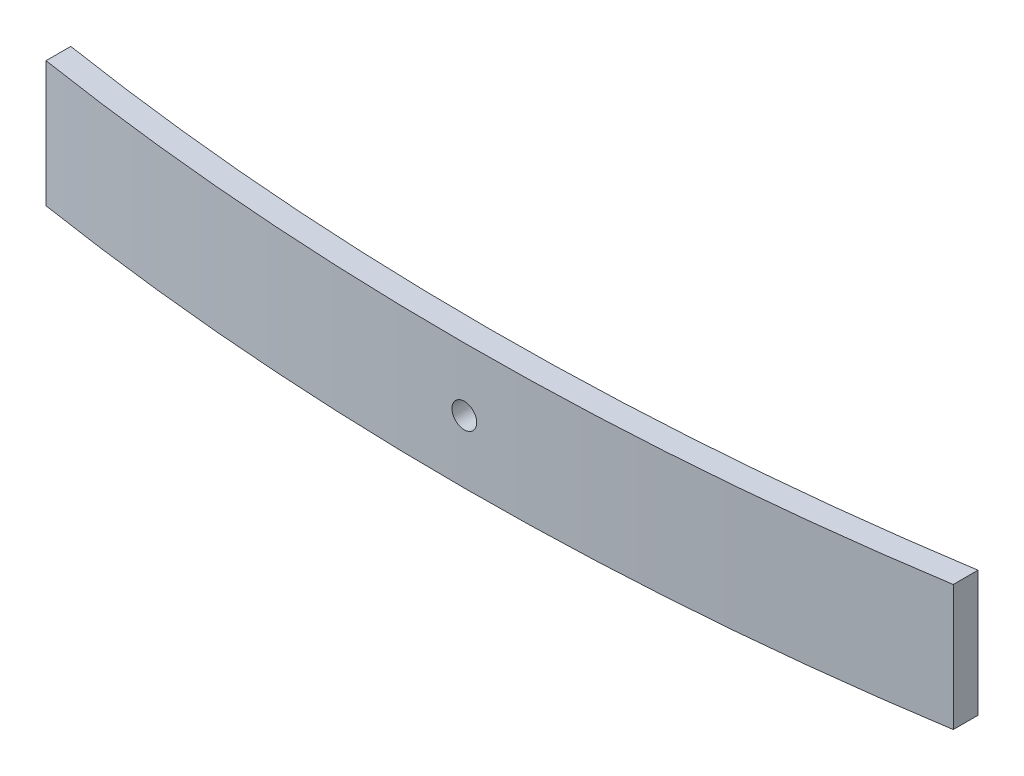
SolidWorks part; units mm, degrees
ref_plane "Front Plane" through (0, 0, 0) normal (0, 0, 1) x (1, 0, 0)
ref_plane "Top Plane" through (0, 0, 0) normal (0, 1, 0) x (1, 0, 0)
ref_plane "Right Plane" through (0, 0, 0) normal (1, 0, 0) x (0, 0, -1)
sketch "Sketch1" plane through (0, 0, 0) normal (0, 1, 0) x (1, 0, 0)
  line L0 (-630, 0) -> (630, 0) construction
  line L1 (-210.8013, -133) -> (245.5549, -133) construction
  line L2 (0, 0) -> (0, -133) construction
  line L3 (-602.5798, 17.4465) -> (-589.9243, 25.4988)
  line L4 (-616.835, -11.5296) -> (-605.5506, -21.4121)
  line L5 (616.835, -11.5296) -> (605.5506, -21.4121)
  line L6 (-630.0217, -47.5) -> (-630.0217, -62.5)
  line L7 (602.5798, 17.4465) -> (589.9243, 25.4988)
  line L8 (630.0217, -47.5) -> (630.0217, -62.5)
  line L9 (-545.0217, -92.3065) -> (-545.0217, -107.3065)
  line L10 (545.0217, -92.3065) -> (545.0217, -107.3065)
  line L11 (-485.0217, -125.4896) -> (-485.0217, -140.4896)
  line L12 (485.0217, -125.4896) -> (485.0217, -140.4896)
  line L13 (-425.0217, -156.3949) -> (-425.0217, -171.3949)
  line L14 (425.0217, -156.3949) -> (425.0217, -171.3949)
  line L15 (-315.0217, -194.8387) -> (-315.0217, -209.8387)
  line L16 (315.0217, -194.8387) -> (315.0217, -209.8387)
  line L17 (-275.0217, -216.5772) -> (-275.0217, -231.5772)
  line L18 (275.0217, -216.5772) -> (275.0217, -231.5772)
  arc A0 (-616.835, -11.5296) -> (-630, -17.5) centre (-630, 0) ccw
  arc A1 (630, -17.5) -> (616.835, -11.5296) centre (630, 0) ccw
  arc A2 (-630, -17.5) -> (630, -17.5) centre (0, 1642.9318) ccw
  arc A3 (-630.0011, -32.5) -> (630.0011, -32.5) centre (0, 1627.9379) ccw
  arc A4 (-605.5506, -21.4121) -> (-630.0011, -32.5) centre (-630, 0) ccw
  arc A5 (630.0011, -32.5) -> (605.5506, -21.4121) centre (630, 0) ccw
  arc A6 (-630.0217, -47.5) -> (630.0217, -47.5) centre (0, 1613.05) ccw
  arc A7 (630.0217, -47.5) -> (589.9243, 25.4988) centre (630, 0) ccw
  arc A8 (-589.9243, 25.4988) -> (-630.0217, -47.5) centre (-630, 0) ccw
  arc A9 (-630.0217, -62.5) -> (630.0217, -62.5) centre (0, 1598.05) ccw
  arc A10 (545.0217, -107.3065) -> (-545.0217, -107.3065) centre (0, 1583.05) cw
  arc A11 (485.0217, -140.4896) -> (-485.0217, -140.4896) centre (0, 1568.05) cw
  arc A12 (425.0217, -171.3949) -> (-425.0217, -171.3949) centre (0, 1553.05) cw
  arc A13 (315.0217, -209.8387) -> (-315.0217, -209.8387) centre (0, 1538.05) cw
  arc A14 (275.0217, -231.5772) -> (-275.0217, -231.5772) centre (0, 1523.05) cw
  point P5 (-630.0217, -47.5)
  point P6 (0, -163)
  point P10 (0, -133)
  point P13 (-630.0011, -32.5)
  point P14 (0, -148)
  point P15 (630.0011, -32.5)
  point P20 (630.0217, -47.5)
  point P27 (0, -178)
  point P37 (0, -193)
  point P40 (630.0217, -55)
  point P44 (0, -208)
  point P50 (0, -223)
  point P56 (0, -238)
  point P62 (0, -253)
  dimension "D4" = 35
  dimension "D5" = 35
  dimension "D9" = 15
  dimension "D12" = 15
  dimension "D1" = 133
  dimension "D2" = 630
  dimension "D3" = 630
  dimension "D6" = 15
  dimension "D7" = 15
  dimension "D8" = 15
  dimension "D10" = 15
  dimension "D11" = 15
  dimension "D13" = 15
  dimension "D14" = 15
  dimension "D15" = 15
  dimension "D16" = 85
  dimension "D17" = 15
  dimension "D18" = 15
  dimension "D19" = 85
  dimension "D20" = 60
  dimension "D21" = 15
  dimension "D22" = 15
  dimension "D23" = 15
  dimension "D24" = 60
  dimension "D25" = 15
  dimension "D26" = 60
  dimension "D27" = 15
  dimension "D28" = 60
  dimension "D29" = 15
  dimension "D30" = 15
  dimension "D31" = 110
  dimension "D32" = 15
  dimension "D33" = 110
  dimension "D34" = 15
  dimension "D35" = 40
  dimension "D36" = 15
  dimension "D37" = 15
  dimension "D38" = 40
  dimension "D39" = 15
sketch "Sketch5" plane through (0, 0, 0) normal (0, 0, 1) x (1, 0, 0)
  circle A0 centre (0, 38.1) radius 7.5
  dimension "D2" = 15
  dimension "D1" = 38.1
sketch "Sketch6" plane through (0, 0, 0) normal (0, 0, 1) x (1, 0, 0)
  circle A0 centre (0, 38.1) radius 7.5
sketch "Sketch7" plane through (0, 0, 0) normal (0, 0, 1) x (1, 0, 0)
  circle A0 centre (0, 38.1) radius 7.5
sketch "Sketch8" plane through (0, 0, 0) normal (0, 0, 1) x (1, 0, 0)
  circle A0 centre (0, 38.1) radius 7.5
sketch "Sketch9" plane through (0, 0, 0) normal (0, 0, 1) x (1, 0, 0)
  circle A0 centre (0, 38.1) radius 7.5
sketch "Sketch10" plane through (0, 0, 0) normal (0, 0, 1) x (1, 0, 0)
  circle A0 centre (0, 38.1) radius 7.5
sketch "Sketch11" plane through (0, 0, 0) normal (0, 0, 1) x (1, 0, 0)
  circle A0 centre (0, 38.1) radius 7.5
extrude "Boss-Extrude1" add sketch "Sketch1" along normal blind 76.2 contours A14 L18 A13 L17
sketch "Sketch12" plane through (0, 0, 0) normal (0, 0, 1) x (1, 0, 0)
  circle A0 centre (0, 38.1) radius 7.5
extrude "Cut-Extrude1" cut sketch "Sketch12" along normal through all
